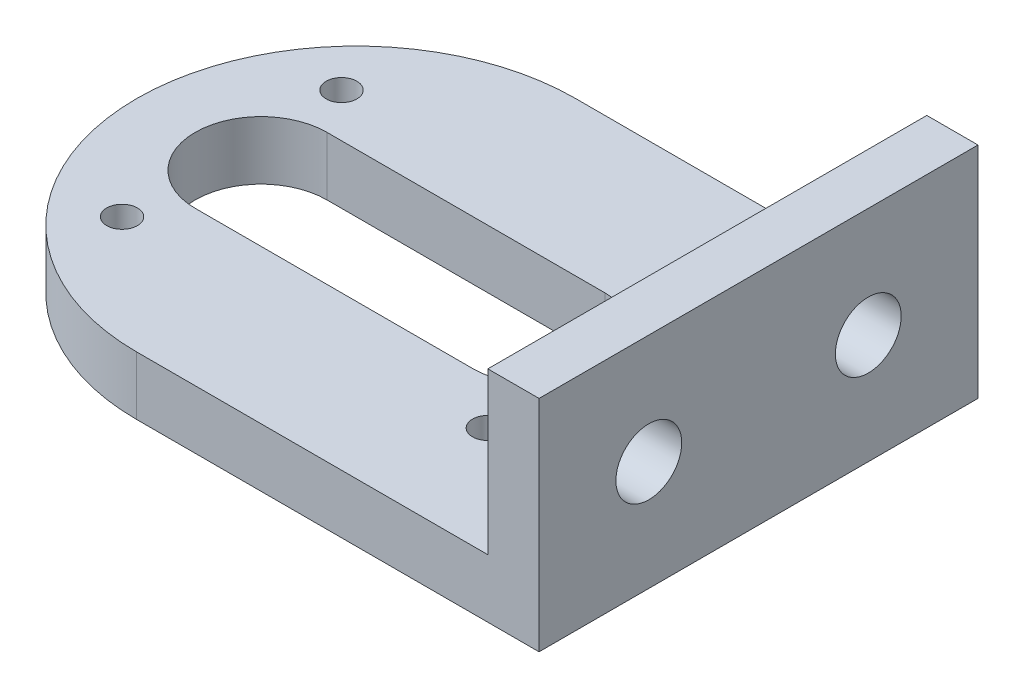
SolidWorks part; units mm, degrees
ref_plane "前视基准面" through (0, 0, 0) normal (0, 0, 1) x (1, 0, 0)
ref_plane "上视基准面" through (0, 0, 0) normal (0, 1, 0) x (1, 0, 0)
ref_plane "右视基准面" through (0, 0, 0) normal (1, 0, 0) x (0, 0, -1)
sketch "草图1" plane through (0, 0, 0) normal (0, 1, 0) x (1, 0, 0)
  line L1 (-14.75, 30) -> (40.25, 30)
  line L3 (-14.75, -30) -> (40.25, -30)
  line L4 (40.25, 30) -> (40.25, -30)
  arc A0 (-14.75, 30) -> (-14.75, -30) centre (-14.75, 0) ccw
  point P0 (0, 0)
  dimension "D4" = 55
  dimension "D1" = 60
  dimension "D2" = 40.25
  dimension "D3" = 30
extrude "凸台-拉伸1" add sketch "草图1" along normal blind 8
sketch "草图2" plane through (0, 8, 0) normal (0, 1, 0) x (1, 0, 0)
  line L0 (-14.75, -30) -> (40.25, -30) construction
  line L1 (40.25, 30) -> (33.25, 30)
  line L2 (40.25, 30) -> (40.25, -30)
  line L3 (40.25, -30) -> (33.25, -30)
  line L4 (33.25, 30) -> (33.25, -30)
  dimension "D1" = 7
extrude "凸台-拉伸2" add sketch "草图2" along normal blind 22
sketch "草图3" plane through (40.25, 0, 0) normal (1, 0, 0) x (0, 0, -1)
  line L0 (-15, 15) -> (15, 15)
  line L1 (-30, 15) -> (-27.4989, 15) construction
  line L2 (-30, 30) -> (-30, 0) construction
  point P6 (0, 15)
  dimension "D1" = 30
  dimension "D2" = 0
hole_wizard "大小mm 暗销孔1" positions "3D草图1" profile "草图4" hole size "Ø1.0" standard "GB" end condition through all
sketch3d "3D草图1"
  point P0 (40.25, 15, 15)
  point P3 (40.25, 15, -15)
sketch "草图4" plane through (40.25, 15, 15) normal (0, 1, 0) x (0, 0, -1)
  line L0 (0, 0) -> (0, 85)
  line L1 (0, 85) -> (4.5, 85)
  line L2 (4.5, 85) -> (4.5, 0)
  line L5 (4.5, 0) -> (0, 0)
  line L11 (0, -6.35) -> (0, 107.95) construction
  dimension "通孔孔直径" = 9
  dimension "通孔孔深度" = 85
sketch "草图5" plane through (0, 0, 0) normal (0, -1, 0) x (1, 0, 0)
  line L0 (-27.75, 0) -> (10.25, 0) construction
  line L1 (-27.75, 9) -> (10.25, 9)
  line L2 (-27.75, -9) -> (10.25, -9)
  line L3 (40.25, 30) -> (40.25, -30) construction
  arc A0 (-27.75, 9) -> (-27.75, -9) centre (-27.75, 0) ccw
  arc A1 (10.25, -9) -> (10.25, 9) centre (10.25, 0) ccw
  point P3 (-8.75, 0)
  point P8 (0, 0)
  point P9 (0, 0)
  dimension "D1" = 18
  dimension "D3" = 38
  dimension "D4" = 30
extrude "切除-拉伸1" cut sketch "草图5" against normal blind 22
sketch "草图6" plane through (0, 0, 0) normal (0, -1, 0) x (1, 0, 0)
  line L0 (40.25, 15) -> (40.25, -15) construction
  line L1 (-31.75, 15) -> (18.25, 15)
  line L2 (-31.75, 15) -> (-31.75, -15)
  line L3 (-31.75, -15) -> (18.25, -15)
  line L4 (18.25, 15) -> (18.25, -15)
  line L5 (-31.75, 15) -> (18.25, -15) construction
  line L6 (-31.75, -15) -> (18.25, 15) construction
  point P0 (-6.75, 0)
  point P6 (0, 0)
  dimension "D1" = 30
  dimension "D2" = 50
  dimension "D3" = 22
  dimension "D4" = 15
hole_wizard "M5 螺纹孔1" positions "3D草图2" profile "草图7" tap size "M5" standard "GB" end condition through all
sketch3d "3D草图2"
  point P0 (-31.75, 0, 15)
  point P3 (18.25, 0, 15)
  point P6 (18.25, 0, -15)
  point P9 (-31.75, 0, -15)
sketch "草图7" plane through (-31.75, 0, 15) normal (1, 0, 0) x (0, 0, -1)
  line L0 (0, 0) -> (0, 30)
  line L1 (0, 30) -> (2.1, 30)
  line L2 (2.1, 30) -> (2.1, 0)
  line L5 (2.1, 0) -> (0, 0)
  line L11 (0, -6.35) -> (0, 107.95) construction
  dimension "通孔螺纹孔钻头直径" = 4.2
  dimension "通孔螺纹孔钻头深度" = 30
cosmetic thread "孔螺蚊线1" parameters "D2"=5
cosmetic thread "孔螺蚊线2" parameters "D2"=5
cosmetic thread "孔螺蚊线3" parameters "D2"=5
cosmetic thread "孔螺蚊线4" parameters "D2"=5
